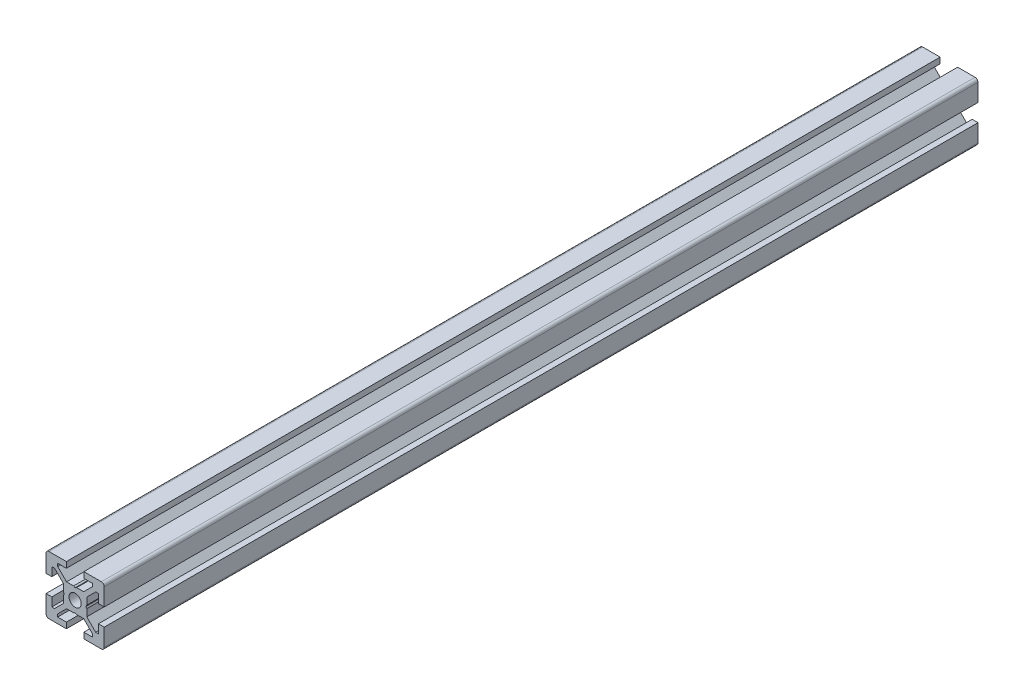
SolidWorks part; units mm, degrees
material "2014 合金"
ref_plane "正面" through (0, 0, 0) normal (0, 0, 1) x (1, 0, 0)
ref_plane "平面" through (0, 0, 0) normal (0, 1, 0) x (1, 0, 0)
ref_plane "右側面" through (0, 0, 0) normal (1, 0, 0) x (0, 0, -1)
ref_plane "平面1" through (0, 0, 0) normal (0, 0, 1) x (1, 0, 0)
sketch "ｽｹｯﾁ1" plane through (0, 0, 0) normal (0, 0, 1) x (1, 0, 0)
  line L0 (-10, -3) -> (-10, -9)
  line L1 (-9, -10) -> (-3, -10)
  line L2 (-3, -10) -> (-3, -8)
  line L3 (-3, -8) -> (-6, -8)
  line L4 (-6, -8) -> (-6, -7.0607)
  line L5 (-6, -7.0607) -> (-2.9393, -4)
  line L6 (-2.9393, -4) -> (-0.5196, -4)
  line L7 (-0.5196, -4) -> (0, -3.7)
  line L8 (0, -3.7) -> (0.5196, -4)
  line L9 (0.5196, -4) -> (2.9393, -4)
  line L10 (2.9393, -4) -> (6, -7.0607)
  line L11 (6, -7.0607) -> (6, -8)
  line L12 (6, -8) -> (3, -8)
  line L13 (3, -8) -> (3, -10)
  line L14 (3, -10) -> (9, -10)
  line L15 (10, -9) -> (10, -3)
  line L16 (10, -3) -> (8, -3)
  line L17 (8, -3) -> (8, -6)
  line L18 (8, -6) -> (7.0607, -6)
  line L19 (7.0607, -6) -> (4, -2.9393)
  line L20 (4, -2.9393) -> (4, -0.5196)
  line L21 (4, -0.5196) -> (3.7, 0)
  line L22 (3.7, 0) -> (4, 0.5196)
  line L23 (4, 0.5196) -> (4, 2.9393)
  line L24 (4, 2.9393) -> (7.0607, 6)
  line L25 (7.0607, 6) -> (8, 6)
  line L26 (8, 6) -> (8, 3)
  line L27 (8, 3) -> (10, 3)
  line L28 (10, 3) -> (10, 9)
  line L29 (9, 10) -> (3, 10)
  line L30 (3, 10) -> (3, 8)
  line L31 (3, 8) -> (6, 8)
  line L32 (6, 8) -> (6, 7.0607)
  line L33 (6, 7.0607) -> (2.9393, 4)
  line L34 (2.9393, 4) -> (0.5196, 4)
  line L35 (0.5196, 4) -> (0, 3.7)
  line L36 (0, 3.7) -> (-0.5196, 4)
  line L37 (-0.5196, 4) -> (-2.9393, 4)
  line L38 (-2.9393, 4) -> (-6, 7.0607)
  line L39 (-6, 7.0607) -> (-6, 8)
  line L40 (-6, 8) -> (-3, 8)
  line L41 (-3, 8) -> (-3, 10)
  line L42 (-3, 10) -> (-9, 10)
  line L43 (-10, 9) -> (-10, 3)
  line L44 (-10, 3) -> (-8, 3)
  line L45 (-8, 3) -> (-8, 6)
  line L46 (-8, 6) -> (-7.0607, 6)
  line L47 (-7.0607, 6) -> (-4, 2.9393)
  line L48 (-4, 2.9393) -> (-4, 0.5196)
  line L49 (-4, 0.5196) -> (-3.7, 0)
  line L50 (-3.7, 0) -> (-4, -0.5196)
  line L51 (-4, -0.5196) -> (-4, -2.9393)
  line L52 (-4, -2.9393) -> (-7.0607, -6)
  line L53 (-7.0607, -6) -> (-8, -6)
  line L54 (-8, -6) -> (-8, -3)
  line L55 (-8, -3) -> (-10, -3)
  arc A0 (-10, -9) -> (-9, -10) centre (-9, -9) ccw
  arc A1 (9, -10) -> (10, -9) centre (9, -9) ccw
  arc A2 (10, 9) -> (9, 10) centre (9, 9) ccw
  arc A3 (-9, 10) -> (-10, 9) centre (-9, 9) ccw
extrude "ﾎﾞｽ - 押し出し1" add sketch "ｽｹｯﾁ1" against normal blind 300
ref_plane "平面2" through (0, 0, 0) normal (1, 0, 0) x (0, 0, -1)
sketch "ｽｹｯﾁ2" plane through (0, 0, 0) normal (1, 0, 0) x (0, 0, -1)
  line L0 (0, 0) -> (0, 2.1)
  line L1 (0, 2.1) -> (260, 2.1)
  line L2 (260, 2.1) -> (260, 0)
  line L3 (260, 0) -> (0, 0)
  line L4 (260, 0) -> (0, 0) construction
revolve "ｶｯﾄ - 回転1" cut sketch "ｽｹｯﾁ2" angle 360 about L4
